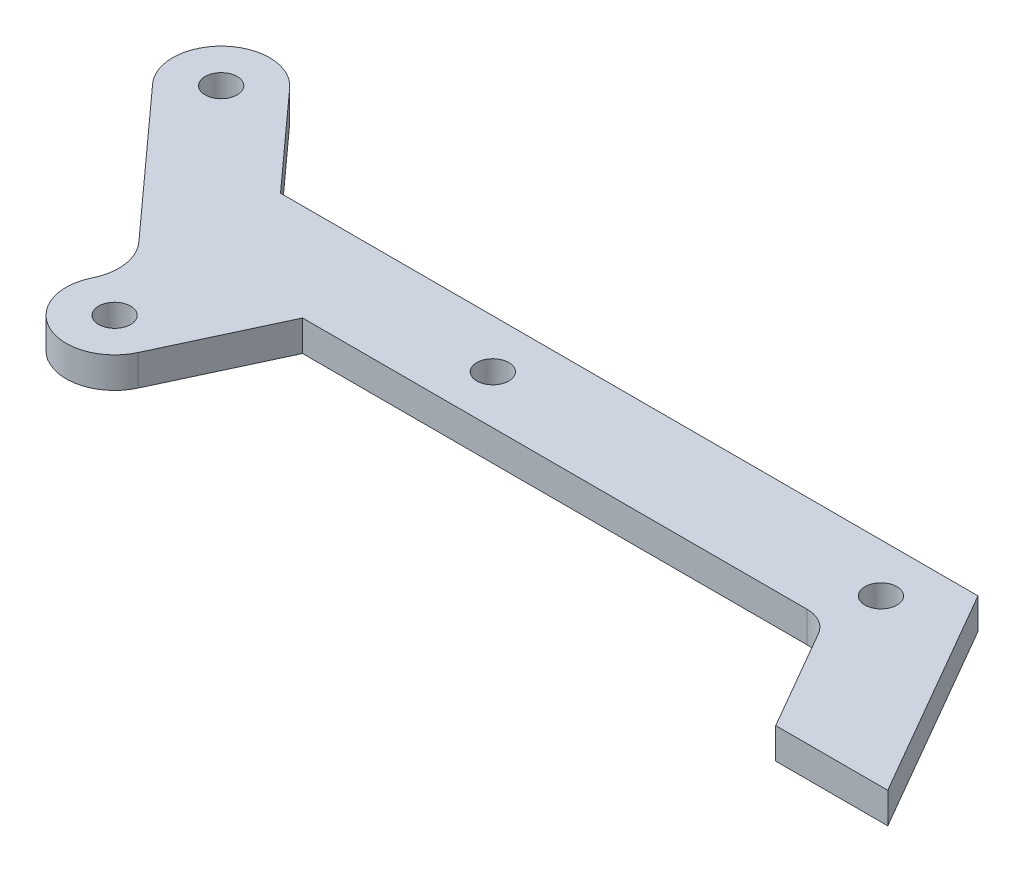
SolidWorks part; units mm, degrees
material "6061-T6 (SS)"
ref_plane "Front Plane" through (0, 0, 0) normal (0, 0, 1) x (1, 0, 0)
ref_plane "Top Plane" through (0, 0, 0) normal (0, 1, 0) x (1, 0, 0)
ref_plane "Right Plane" through (0, 0, 0) normal (1, 0, 0) x (0, 0, -1)
sketch "Sketch1" plane through (0, 0, 0) normal (0, 1, 0) x (1, 0, 0)
  line L0 (0, 0) -> (-11.547, 0)
  line L1 (-11.547, 0) -> (-17.5587, 10.4125)
  line L2 (-20.3083, 12) -> (-72.3083, 12)
  line L4 (0, 0) -> (-12.7017, 22)
  line L5 (-12.7017, 22) -> (-84.5799, 22)
  line L8 (-72.3083, 12) -> (-77.6985, 0.4408)
  line L9 (-86.7615, 4.6669) -> (-86.6755, 4.8514)
  line L10 (-87.4985, 10.3181) -> (-100.9386, 25.1811)
  line L12 (-97.23, 28.5346) -> (-82.23, 2.5539) construction
  line L13 (-93.5214, 31.8882) -> (-84.5799, 22)
  arc A0 (-93.5214, 31.8882) -> (-100.9386, 25.1811) centre (-97.23, 28.5346) ccw
  arc A1 (-17.5587, 10.4125) -> (-20.3083, 12) centre (-20.3083, 8.825) ccw
  arc A2 (-77.6985, 0.4408) -> (-86.7615, 4.6669) centre (-82.23, 2.5539) cw
  arc A3 (-86.6755, 4.8514) -> (-87.4985, 10.3181) centre (-91.2071, 6.9645) ccw
  dimension "D6" = 3.175
  dimension "D4" = 5
  dimension "D14" = 5
  dimension "D9" = 5
  dimension "D1" = 10
  dimension "D2" = 10
  dimension "D3" = 120
  dimension "D5" = 12
  dimension "D7" = 30
  dimension "D8" = 60
  dimension "D10" = 115
  dimension "D11" = 10
  dimension "D12" = 52
  dimension "D13" = 10
extrude "Boss-Extrude1" add sketch "Sketch1" along normal mid plane 3.175 contours L5 L13 A0 L10 A3 L9 A2 L8 L2 A1 L1 L0 L4
sketch "Sketch4" plane through (0, 1.5875, 0) normal (0, 1, 0) x (1, 0, 0)
  line L0 (-20.3083, 12) -> (-72.3083, 12) construction
  point P0 (-17.7017, 17)
  point P2 (-57.7017, 17)
  point P5 (0, 0)
  dimension "D1" = 5
  dimension "D2" = 40
  dimension "D3" = 5
hole_wizard "M4x0.7 Tapped Hole1" positions "Sketch4" profile "Sketch5" tap size "M4x0.7" standard "ANSI Metric" end condition through all
sketch "Sketch5" plane through (-17.7017, 1.5875, -17) normal (1, 0, 0) x (0, 0, 1)
  line L0 (0, 0) -> (0, 3.175)
  line L1 (0, 3.175) -> (1.65, 3.175)
  line L2 (1.65, 3.175) -> (1.65, 0)
  line L5 (1.65, 0) -> (0, 0)
  line L11 (0, -6.35) -> (0, 107.95) construction
  dimension "Thru Tap Drill Dia." = 3.3
  dimension "Thru Tap Drill Depth" = 3.175
cosmetic thread "Hole Thread1" parameters "D2"=4
cosmetic thread "Hole Thread2" parameters "D2"=4
sketch "Sketch8" plane through (0, 1.5875, 0) normal (0, 1, 0) x (1, 0, 0)
  arc A0 (-93.5214, 31.8882) -> (-100.9386, 25.1811) centre (-97.23, 28.5346) ccw construction
  arc A2 (-86.7615, 4.6669) -> (-77.6985, 0.4408) centre (-82.23, 2.5539) ccw construction
  point P0 (-82.23, 2.5539)
  point P8 (-97.23, 28.5346)
  point P40 (-86.9654, -3.9003)
  point P41 (-88.7644, -5.0256)
  point P43 (-88.7605, -5.0234)
  point P47 (-89.3346, -5.3466)
  point P48 (-88.5456, -5.4566)
hole_wizard "M4x0.7 Tapped Hole2" positions "Sketch8" profile "Sketch7" tap size "M4x0.7" standard "ANSI Metric" end condition through all
sketch "Sketch7" plane through (-82.23, 1.5875, -2.5539) normal (1, 0, 0) x (0, 0, 1)
  line L0 (0, 0) -> (0, 3.175)
  line L1 (0, 3.175) -> (1.65, 3.175)
  line L2 (1.65, 3.175) -> (1.65, 0)
  line L5 (1.65, 0) -> (0, 0)
  line L11 (0, -6.35) -> (0, 107.95) construction
  dimension "Thru Tap Drill Dia." = 3.3
  dimension "Thru Tap Drill Depth" = 3.175
cosmetic thread "Hole Thread3" parameters "D2"=4
cosmetic thread "Hole Thread4" parameters "D2"=4
